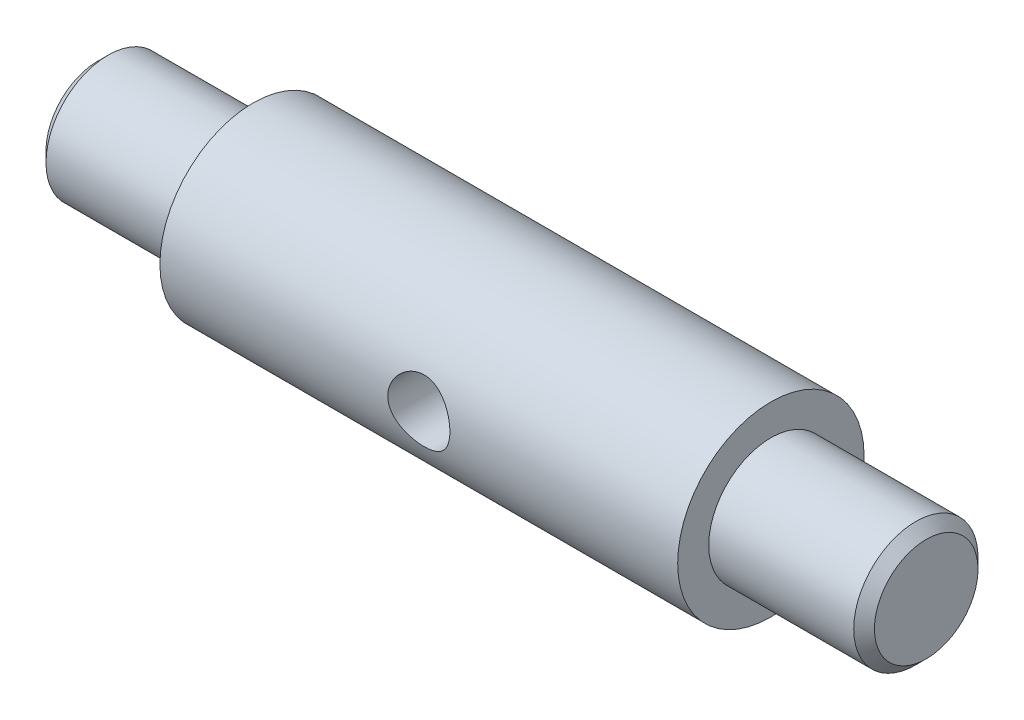
SolidWorks part; units mm, degrees
ref_plane "Front Plane" through (0, 0, 0) normal (0, 0, 1) x (1, 0, 0)
ref_plane "Top Plane" through (0, 0, 0) normal (0, 1, 0) x (1, 0, 0)
ref_plane "Right Plane" through (0, 0, 0) normal (1, 0, 0) x (0, 0, -1)
sketch "Sketch1" plane through (0, 0, 0) normal (0, 0, 1) x (1, 0, 0)
  line L0 (0, 0) -> (80, 0)
  line L1 (80, 0) -> (80, 6)
  line L2 (80, 6) -> (65, 6)
  line L3 (65, 6) -> (65, 9)
  line L4 (65, 9) -> (15, 9)
  line L5 (15, 9) -> (15, 6)
  line L6 (15, 6) -> (0, 6)
  line L7 (0, 6) -> (0, 0)
  dimension "D1" = 80
  dimension "D2" = 15
  dimension "D3" = 9
  dimension "D4" = 6
revolve "Revolve2" add sketch "Sketch1" angle 360 about L0
sketch "Sketch2" plane through (0, 0, 0) normal (0, 0, 1) x (1, 0, 0)
  line L0 (15, 9) -> (15, -9) construction
  circle A0 centre (40, 0) radius 3
  point P4 (0, 0)
  point P5 (0, 0)
  point P6 (0, 0)
  point P7 (0, 0)
  point P10 (0, 0)
  point P11 (0, 0)
  point P12 (0, 0)
  point P13 (0, 0)
  dimension "D1" = 25
extrude "Cut-Extrude1" cut sketch "Sketch2" against normal through all both and the other way through all
chamfer "Chamfer1" distance 1 angle 45 2 edges at (0, 0, 6) (80, 0, 6)
hole_wizard "Ø6.0 (6) Diameter Hole1" positions "Sketch3" profile "Sketch4" hole size "Ø6.0" standard "DIN"
sketch "Sketch3" plane through (0, 0, 0) normal (-1, 0, 0) x (0, 0, 1)
  point P0 (0, 0)
sketch "Sketch4" plane through (0, 0, 0) normal (0, 1, 0) x (0, 0, 1)
  line L0 (0, 0) -> (0, 46.8026)
  line L1 (0, 46.8026) -> (3, 45)
  line L2 (3, 45) -> (3, 0)
  line L5 (3, 0) -> (0, 0)
  line L10 (0, 46.8026) -> (-3, 45) construction
  line L11 (0, -6.35) -> (0, 107.95) construction
  dimension "Hole Dia." = 6
  dimension "Hole Depth" = 45
  dimension "Drill Angle" = 118
